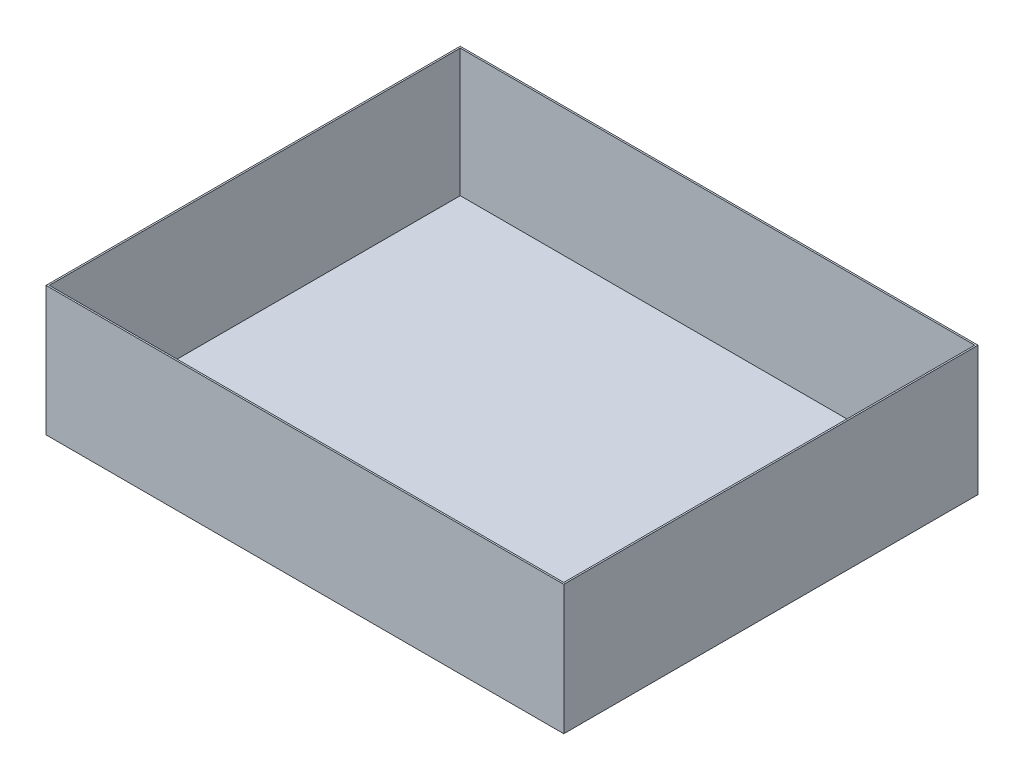
SolidWorks part; units mm, degrees
ref_plane "Front Plane" through (0, 0, 0) normal (0, 0, 1) x (1, 0, 0)
ref_plane "Top Plane" through (0, 0, 0) normal (0, 1, 0) x (1, 0, 0)
ref_plane "Right Plane" through (0, 0, 0) normal (1, 0, 0) x (0, 0, -1)
sketch "Sketch1" plane through (0, 0, 0) normal (0, 1, 0) x (1, 0, 0)
  line L1 (0, 0) -> (254, 0)
  line L2 (0, 0) -> (0, 203.2)
  line L3 (0, 203.2) -> (254, 203.2)
  line L4 (254, 0) -> (254, 203.2)
extrude "Boss-Extrude1" add sketch "Sketch1" along normal blind 63.5
shell "Shell3" thickness 0.7937
